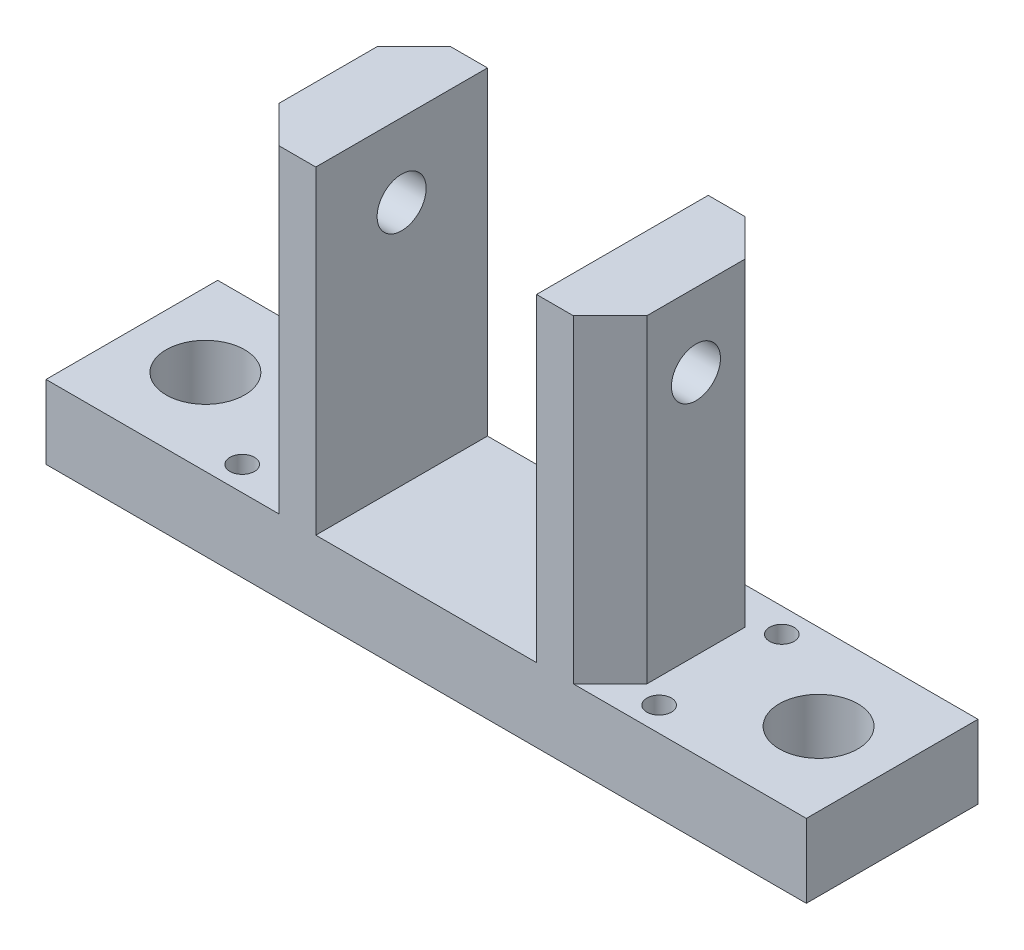
SolidWorks part; units mm, degrees
ref_plane "Plan de face" through (0, 0, 0) normal (0, 0, 1) x (1, 0, 0)
ref_plane "Plan de dessus" through (0, 0, 0) normal (0, 1, 0) x (1, 0, 0)
ref_plane "Plan de droite" through (0, 0, 0) normal (1, 0, 0) x (0, 0, -1)
sketch "Esquisse1" plane through (0, 0, 0) normal (0, 0, 1) x (1, 0, 0)
  line L0 (0, 0) -> (-31, 0)
  line L1 (-31, 0) -> (-31, 3)
  line L2 (-31, 3) -> (-23, 3)
  line L3 (-23, 3) -> (-23, 16)
  line L4 (-23, 16) -> (-20, 16)
  line L5 (-20, 16) -> (-20, 3)
  line L6 (-20, 3) -> (-11, 3)
  line L7 (-11, 3) -> (-11, 16)
  line L8 (-11, 16) -> (-8, 16)
  line L9 (-8, 16) -> (-8, 3)
  line L10 (-8, 3) -> (0, 3)
  line L11 (0, 3) -> (0, 0)
  dimension "D1" = 3
  dimension "D2" = 16
  dimension "D3" = 11
  dimension "D4" = 3
  dimension "D5" = 31
extrude "Extrusion1" add sketch "Esquisse1" along normal mid plane 7
sketch "Esquisse2" plane through (0, 3, 0) normal (0, 1, 0) x (-1, 0, 0)
  line L0 (31, 0) -> (28, 0) construction
  line L1 (31, 3.5) -> (31, -3.5) construction
  line L2 (28, 0) -> (3, 0) construction
  line L3 (3, 0) -> (0, 0) construction
  line L4 (24, -2.5) -> (24, 0) construction
  line L5 (24, 0) -> (24, 2.5) construction
  line L6 (7, -2.5) -> (7, 0) construction
  line L7 (7, 0) -> (7, 2.5) construction
  line L8 (23, 3.5) -> (23, -3.5) construction
  line L9 (8, 3.5) -> (8, -3.5) construction
  circle A0 centre (28, 0) radius 1.6
  circle A1 centre (3, 0) radius 1.6
  circle A2 centre (24, -2.5) radius 0.5
  circle A3 centre (24, 2.5) radius 0.5
  circle A4 centre (7, 2.5) radius 0.5
  circle A5 centre (7, -2.5) radius 0.5
  dimension "D1" = 3.2
  dimension "D6" = 1
  dimension "D2" = 2.5
  dimension "D3" = 1
  dimension "D4" = 1
  dimension "D5" = 25
extrude "Enlèv. mat.-Extru.1" cut sketch "Esquisse2" against normal through all
sketch "Esquisse3" plane through (-23, 0, 0) normal (-1, 0, 0) x (0, 0, 1)
  line L0 (0, 16) -> (0, 13)
  line L1 (3.5, 16) -> (-3.5, 16) construction
  circle A0 centre (0, 13) radius 1
  dimension "D1" = 2
  dimension "D2" = 3
extrude "Enlèv. mat.-Extru.2" cut sketch "Esquisse3" against normal through all
chamfer "Chanfrein1" distance 1.5 angle 45 4 edges at (-8, 9.5, 3.5) (-23, 9.5, -3.5) (-8, 9.5, -3.5) (-23, 9.5, 3.5)
